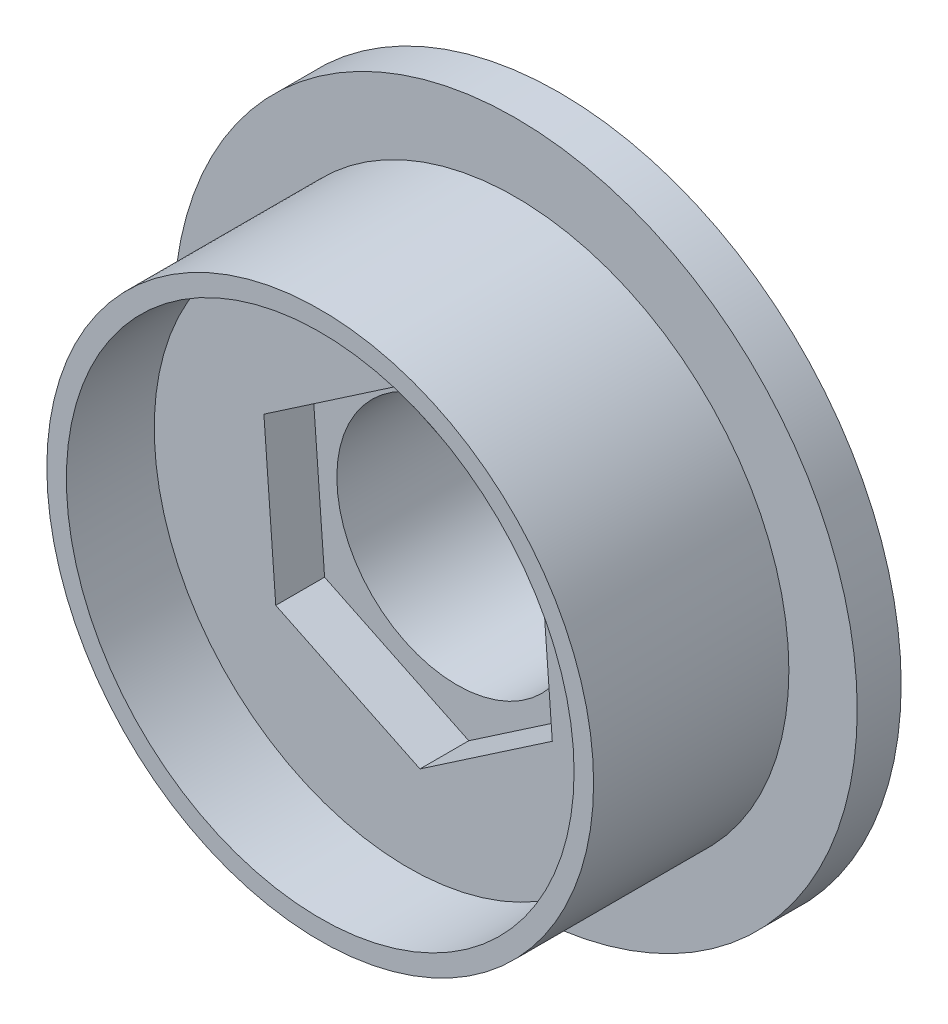
SolidWorks part; units mm, degrees
ref_plane "Front Plane" through (0, 0, 0) normal (0, 0, 1) x (1, 0, 0)
ref_plane "Top Plane" through (0, 0, 0) normal (0, 1, 0) x (1, 0, 0)
ref_plane "Right Plane" through (0, 0, 0) normal (1, 0, 0) x (0, 0, -1)
sketch "Sketch1" plane through (0, 0, 0) normal (0, 1, 0) x (1, 0, 0)
  line L0 (0, 0) -> (0, -14.25) construction
  line L1 (6.15, -14.25) -> (6.15, 0)
  line L2 (17.5, -4.25) -> (17.5, -2)
  line L3 (14, -14.25) -> (6.15, -14.25)
  line L4 (6.15, 0) -> (0, 0) construction
  line L5 (6.15, -14.25) -> (0, -14.25) construction
  line L6 (17.5, -4.25) -> (14, -4.25)
  line L7 (14, -4.25) -> (14, -14.25)
  line L8 (6.15, 0) -> (8, 0)
  arc A1 (8, 0) -> (17.5, -2) centre (8, -23.5625) cw
  point P10 (7.2525, 0)
  dimension "D1" = 6.15
  dimension "D2" = 14
  dimension "D3" = 14.25
  dimension "D4" = 2
  dimension "D5" = 8
  dimension "D6" = 17.5
  dimension "D7" = 10
revolve "Revolve1" add sketch "Sketch1" angle 360 about L0
sketch "Sketch3" plane through (0, 0, 14.25) normal (0, 0, 1) x (1, 0, 0)
  line L1 (0.6085, -8.3169) -> (7.3847, -3.7021)
  line L2 (7.3847, -3.7021) -> (6.7762, 4.4737)
  line L3 (6.7762, 4.4737) -> (-0.6085, 8.0346)
  line L4 (-0.6085, 8.0346) -> (-7.3847, 3.4198)
  line L5 (-7.3847, 3.4198) -> (-6.7762, -4.756)
  line L6 (-6.7762, -4.756) -> (0.6085, -8.3169)
  circle A0 centre (0, -0.1411) radius 7.1 construction
  dimension "D1" = 14.2
extrude "Cut-Extrude2" cut sketch "Sketch3" against normal offset from surface (7 mm away) 7.25 up to face at (-6.15, 0, 0)
sketch "Sketch2" plane through (0, 0, 14.25) normal (0, 0, 1) x (1, 0, 0)
  circle A2 centre (0, 0) radius 13
  dimension "D1" = 26
extrude "Cut-Extrude1" cut sketch "Sketch2" against normal offset from surface (4.5 mm away) 9.75 up to face at (-6.15, 0, 0)
